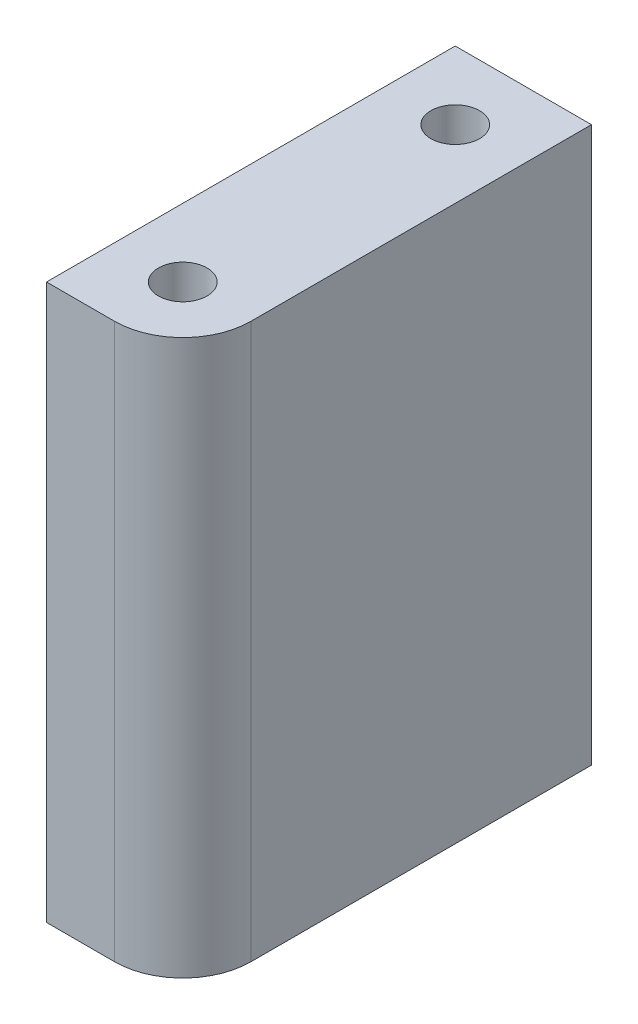
SolidWorks part; units mm, degrees
ref_plane "前视基准面" through (0, 0, 0) normal (0, 0, 1) x (1, 0, 0)
ref_plane "上视基准面" through (0, 0, 0) normal (0, 1, 0) x (1, 0, 0)
ref_plane "右视基准面" through (0, 0, 0) normal (1, 0, 0) x (0, 0, -1)
sketch "草图1" plane through (0, 0, 0) normal (0, 1, 0) x (1, 0, 0)
  line L0 (0, 14) -> (0, -14) construction
  line L2 (-7, 21) -> (7, 21)
  line L3 (-7, 21) -> (-7, -21)
  line L4 (-7, -21) -> (0, -21)
  line L5 (7, 21) -> (7, -14)
  line L6 (-7, 21) -> (7, -21) construction
  line L7 (-7, -21) -> (7, 21) construction
  circle A0 centre (0, 14) radius 2.5
  circle A1 centre (0, -14) radius 2.5
  arc A2 (0, -21) -> (7, -14) centre (0, -14) ccw
  point P4 (0, 0)
  point P8 (0, 0)
  dimension "D1" = 5
  dimension "D3" = 7
  dimension "D5" = 7
  dimension "D2" = 42
  dimension "D4" = 7
extrude "凸台-拉伸1" add sketch "草图1" along normal blind 57
